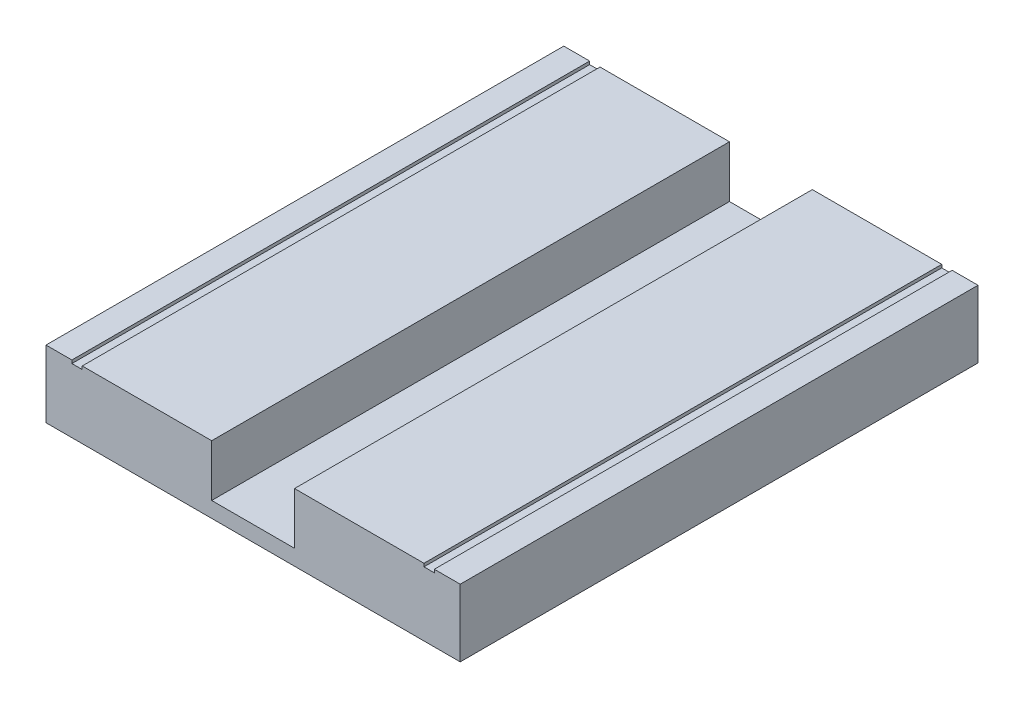
SolidWorks part; units mm, degrees
ref_plane "Plan de face" through (0, 0, 0) normal (0, 0, 1) x (1, 0, 0)
ref_plane "Plan de dessus" through (0, 0, 0) normal (0, 1, 0) x (1, 0, 0)
ref_plane "Plan de droite" through (0, 0, 0) normal (1, 0, 0) x (0, 0, -1)
sketch "Esquisse3" plane through (0, 0, 0) normal (0, 0, 1) x (1, 0, 0)
  line L0 (-40, 0) -> (40, 0)
  dimension "D1" = 40
  dimension "D2" = 40
extrude "Extru.-Mince4" add sketch "Esquisse3" along normal blind 100 thin
sketch "Esquisse4" plane through (0, 0, 0) normal (0, 1, 0) x (1, 0, 0)
  line L0 (-35, 0) -> (-35, -100)
  line L1 (-40, 0) -> (40, 0) construction
  line L2 (-40, -100) -> (40, -100) construction
  line L3 (-35, -100) -> (-33, -100)
  line L4 (-33, -100) -> (-33, 0)
  line L5 (-33, 0) -> (-35, 0)
  line L6 (0, 0) -> (0, -100) construction
  line L7 (35, -100) -> (33, -100)
  line L8 (33, -100) -> (33, 0)
  line L9 (35, 0) -> (35, -100)
  line L10 (33, 0) -> (35, 0)
  dimension "D1" = 5
  dimension "D2" = 2
extrude "Enlèv. mat.-Extru.1" cut sketch "Esquisse4" against normal blind 0.6
sketch "Esquisse5" plane through (0, 0, 0) normal (0, 1, 0) x (1, 0, 0)
  line L0 (0, 0) -> (-8, 0)
  line L1 (-33, 0) -> (33, 0) construction
  line L2 (-8, 0) -> (-8, -100)
  line L3 (-33, -100) -> (33, -100) construction
  line L4 (-8, -100) -> (8, -100)
  line L5 (8, -100) -> (8, 0)
  line L6 (8, 0) -> (0, 0)
  dimension "D1" = 8
  dimension "D2" = 8
extrude "Enlèv. mat.-Extru.2" cut sketch "Esquisse5" against normal blind 11
sketch "Esquisse6" plane through (0, -10, 0) normal (0, -1, 0) x (1, 0, 0)
  line L7 (40, 0) -> (-40, 0)
  line L8 (40, 0) -> (40, 100)
  line L9 (40, 100) -> (-40, 100)
  line L10 (-40, 0) -> (-40, 100)
extrude "Boss.-Extru.1" add sketch "Esquisse6" along normal blind 3
